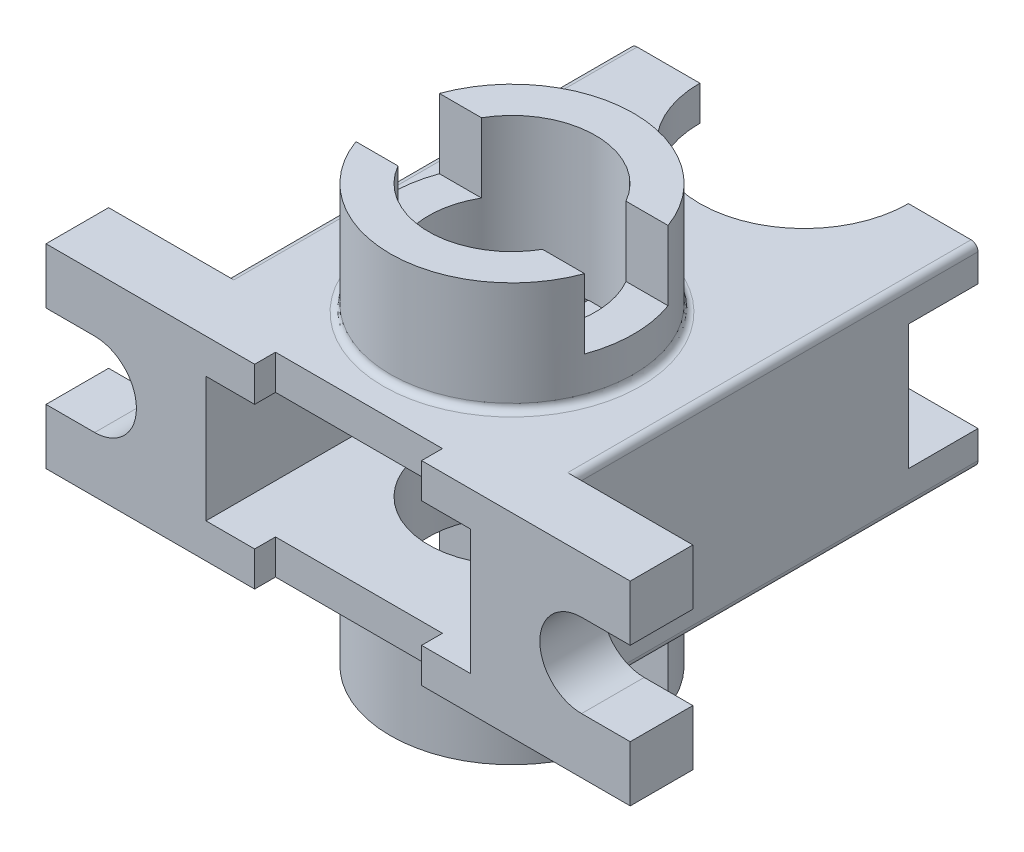
SolidWorks part; units mm, degrees
ref_plane "Front Plane" through (0, 0, 0) normal (0, 0, 1) x (1, 0, 0)
ref_plane "Top Plane" through (0, 0, 0) normal (0, 1, 0) x (1, 0, 0)
ref_plane "Right Plane" through (0, 0, 0) normal (1, 0, 0) x (0, 0, -1)
sketch "Sketch1" plane through (0, 0, 0) normal (0, 1, 0) x (1, 0, 0)
  circle A0 centre (0, 0) radius 17.5
  circle A1 centre (0, 0) radius 12
  dimension "D1" = 35
  dimension "D2" = 24
extrude "Boss-Extrude1" add sketch "Sketch1" along normal mid plane 60
sketch "Sketch5" plane through (0, 0, 0) normal (0, 1, 0) x (1, 0, 0)
  line L0 (-42, -25) -> (-12, -25)
  line L1 (-12, -25) -> (-12, -22)
  line L2 (-12, -22) -> (12, -22)
  line L3 (12, -22) -> (12, -25)
  line L4 (12, -25) -> (42, -25)
  line L5 (42, -25) -> (42, -16)
  line L6 (42, -16) -> (-42, -16)
  line L7 (-42, -16) -> (-42, -25)
  line L8 (-25, -16) -> (-25, 42)
  line L9 (-25, 42) -> (-15, 42)
  line L10 (15, 42) -> (25, 42)
  line L11 (25, 42) -> (25, -16)
  line L12 (0, 0) -> (0, -6.7957) construction
  circle A0 centre (0, 0) radius 12 construction
  arc A1 (-15, 42) -> (15, 42) centre (0, 42) ccw
  circle A2 centre (0, 0) radius 17.5 construction
  arc A3 (7.0887, -16) -> (-7.0887, -16) centre (0, 0) ccw
  point P10 (0, -16)
  point P12 (0, -22)
  point P22 (0, 0)
  point P23 (0, 28.2162)
  dimension "D2" = 25
  dimension "D7" = 15
  dimension "D1" = 9
  dimension "D3" = 84
  dimension "D4" = 24
  dimension "D5" = 3
  dimension "D6" = 50
  dimension "D8" = 10
  dimension "D9" = 67
extrude "Boss-Extrude2" add sketch "Sketch5" along normal mid plane 28 contours L6 L7 L0 L1 L2 L3 L4 L5 | A3 L6 L11 L10 A1 L9 L8
sketch "Sketch6" plane through (0, 0, 16) normal (0, 0, -1) x (-1, 0, 0)
  line L0 (35, 0) -> (49, 0) construction
  line L1 (35, 6) -> (49, 6)
  line L2 (35, -6) -> (49, -6)
  line L3 (42, 14) -> (42, -14) construction
  line L4 (0, 0) -> (0, -12.6637) construction
  line L5 (-35, 0) -> (-49, 0) construction
  line L6 (-35, 6) -> (-49, 6)
  line L7 (-35, -6) -> (-49, -6)
  arc A0 (35, 6) -> (35, -6) centre (35, 0) ccw
  arc A1 (49, -6) -> (49, 6) centre (49, 0) ccw
  arc A2 (-35, 6) -> (-35, -6) centre (-35, 0) cw
  arc A3 (-49, -6) -> (-49, 6) centre (-49, 0) cw
  point P3 (42, 0)
  point P14 (-42, 0)
  dimension "D1" = 12
  dimension "D2" = 70
extrude "Cut-Extrude1" cut sketch "Sketch6" against normal through all
sketch "Sketch8" plane through (0, 0, 0) normal (1, 0, 0) x (0, 0, -1)
  line L0 (42, 14) -> (42, -14) construction
  line L1 (-42, 9) -> (42, 9)
  line L2 (-42, 9) -> (-42, -9)
  line L3 (-42, -9) -> (42, -9)
  line L4 (42, 9) -> (42, -9)
  line L5 (-42, 9) -> (42, -9) construction
  line L6 (-42, -9) -> (42, 9) construction
  point P0 (0, 0)
  dimension "D1" = 18
extrude "Cut-Extrude2" cut sketch "Sketch8" against normal mid plane 38
sketch "Sketch9" plane through (-25, 0, 0) normal (-1, 0, 0) x (0, 0, 1)
  line L0 (-42, 14) -> (-42, -14) construction
  line L1 (-42, -9) -> (-32, -9)
  line L2 (-42, -9) -> (-42, 9)
  line L3 (-42, 9) -> (-32, 9)
  line L4 (-32, -9) -> (-32, 9)
  point P6 (-42, 0)
  dimension "D1" = 18
  dimension "D2" = 10
extrude "Cut-Extrude3" cut sketch "Sketch9" against normal through all
sketch "Sketch10" plane through (0, 0, 0) normal (1, 0, 0) x (0, 0, -1)
  line L0 (-17.5, -30) -> (17.5, -30) construction
  line L1 (6, -30) -> (-6, -30)
  line L2 (6, -30) -> (6, -20)
  line L3 (6, -20) -> (-6, -20)
  line L4 (-6, -30) -> (-6, -20)
  line L5 (0, 0) -> (15.2367, 0) construction
  line L6 (-6, 30) -> (-6, 20)
  line L7 (6, 20) -> (-6, 20)
  line L8 (6, 30) -> (6, 20)
  line L9 (6, 30) -> (-6, 30)
  point P6 (0, -20)
  dimension "D1" = 12
  dimension "D2" = 10
extrude "Cut-Extrude4" cut sketch "Sketch10" against normal through all both and the other way through all
sketch "Sketch7" plane through (-25, 0, 0) normal (-1, 0, 0) x (0, 0, 1)
  line L0 (25, -6) -> (25, -14) construction
  circle A0 centre (-12, 0) radius 4
  point P4 (0, 0)
  point P6 (-12, 0)
  dimension "D1" = 37
  dimension "D2" = 8
extrude "Cut-Extrude5" cut sketch "Sketch7" against normal up to next
fillet "Fillet2" radius 1 6 edges at (25, 14, -13) (25, -14, -13) (0, -14, 17.5) (0, 14, 17.5) (-25, 14, -13) (-25, -14, -13)
